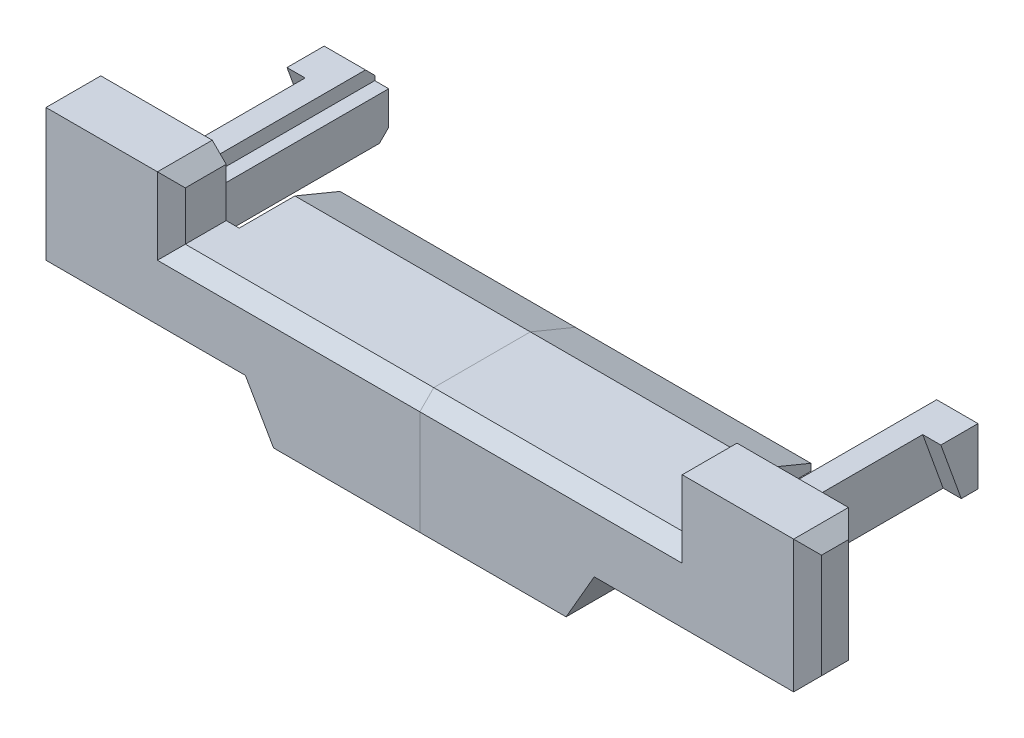
SolidWorks part; units mm, degrees
ref_plane "Płaszczyzna przednia" through (0, 0, 0) normal (0, 0, 1) x (1, 0, 0)
ref_plane "Płaszczyzna górna" through (0, 0, 0) normal (0, 1, 0) x (1, 0, 0)
ref_plane "Płaszczyzna prawa" through (0, 0, 0) normal (1, 0, 0) x (0, 0, -1)
sketch "Sketch1" plane through (0, 0, 0) normal (0, 0, 1) x (1, 0, 0)
  line L0 (-8.2, 0.6) -> (-8.2, 1.95)
  line L1 (-8.2, 1.95) -> (-11.2, 1.95)
  line L2 (-11.2, 1.95) -> (-11.2, -0.9)
  line L3 (-11.2, -0.9) -> (-6.6062, -0.9)
  line L4 (-6.6062, -0.9) -> (-6, -1.95)
  line L5 (-6, -1.95) -> (6, -1.95)
  line L6 (6, -1.95) -> (6.6062, -0.9)
  line L7 (6.6062, -0.9) -> (11.2, -0.9)
  line L8 (11.2, -0.9) -> (11.2, 1.95)
  line L9 (11.2, 1.95) -> (8.2, 1.95)
  line L10 (8.2, 1.95) -> (8.2, 0.6)
  line L11 (8.2, 0.6) -> (-8.2, 0.6)
extrude "Boss-Extrude1" add sketch "Sketch1" along normal blind 1.18
sketch "Sketch2" plane through (0, 0.6, 0) normal (0, 1, 0) x (1, 0, 0)
  line L0 (0, -1.18) -> (0, 2.17) construction
  line L1 (8.2, -1.18) -> (-8.2, -1.18) construction
  line L2 (7.92, 0) -> (7.92, 2.17)
  line L3 (8.2, 0) -> (-8.2, 0) construction
  line L4 (7.92, 2.17) -> (-7.92, 2.17)
  line L5 (-7.92, 2.17) -> (-7.92, 0)
  line L6 (8.2, -1.18) -> (8.2, 0) construction
  line L7 (7.92, 0) -> (-7.92, 0)
  dimension "D1" = 0.28
  dimension "D2" = 2.17
extrude "Boss-Extrude2" add sketch "Sketch2" against normal blind 0.55
sketch "Sketch3" plane through (-7.92, 0, 0) normal (-1, 0, 0) x (0, 0, 1)
  line L0 (-1.2, 0.6) -> (-2.17, 0.2)
  line L1 (-2.17, 0.6) -> (0, 0.6) construction
  line L2 (-2.17, 0.05) -> (-2.17, 0.6) construction
  line L3 (-2.17, 0.2) -> (-2.17, 0.6)
  line L4 (-2.17, 0.6) -> (-1.2, 0.6)
  dimension "D1" = 0.97
  dimension "D2" = 0.4
extrude "Cut-Extrude1" cut sketch "Sketch3" against normal through all both and the other way through all
chamfer "Chamfer1" distance 0.3 angle 45 8 edges at (11.2, -0.9, 0.59) (11.2, 0.525, 1.18) (11.2, 1.95, 0.59) (11.2, 0.525, 0) (-11.2, 1.95, 0.59) (-11.2, 0.525, 1.18) (-11.2, -0.9, 0.59) (-11.2, 0.525, 0)
chamfer "Chamfer2" distance 0.3 angle 45 5 edges at (-8.2, 1.95, 0.59) (-8.2, 1.275, 1.18) (8.2, 1.95, 0.59) (8.2, 1.275, 1.18) (0, 0.6, 1.18)
sketch "Sketch4" plane through (0, 0, 0) normal (0, 0, -1) x (-1, 0, 0)
  line L0 (-10.9, 1.95) -> (-8.5, 1.95) construction
  line L1 (-9.89, -0.11) -> (-8.7, -0.11)
  line L2 (-9.89, -0.11) -> (-9.89, 1.11)
  line L3 (-9.89, 1.11) -> (-8.7, 1.11)
  line L4 (-8.7, -0.11) -> (-8.7, 1.11)
  line L5 (-9.89, -0.11) -> (-8.7, 1.11) construction
  line L6 (-9.89, 1.11) -> (-8.7, -0.11) construction
  line L7 (-11.2, -0.6) -> (-11.2, 1.65) construction
  point P0 (-9.295, 0.5)
  dimension "D1" = 1.22
  dimension "D2" = 1.19
  dimension "D3" = 0.84
  dimension "D4" = 1.31
extrude "Boss-Extrude3" add sketch "Sketch4" along normal blind 4 separate body
sketch "Sketch5" plane through (0, 0, -4) normal (0, 0, -1) x (-1, 0, 0)
  line L0 (-9, 1.11) -> (-9, 0.81)
  line L1 (-8.7, 1.11) -> (-9.89, 1.11) construction
  line L2 (-9, 0.81) -> (-8.7, 0.81)
  line L3 (-8.7, -0.11) -> (-8.7, 1.11) construction
  line L4 (-8.7, 0.81) -> (-8.7, 1.11)
  line L5 (-8.7, 1.11) -> (-9, 1.11)
  dimension "D1" = 0.3
  dimension "D2" = 0.3
extrude "Cut-Extrude2" cut sketch "Sketch5" against normal up to surface (4 mm away) up to face at (0, 0.3389, 0)
chamfer "Chamfer3" distance 0.2 angle 45 3 edges at (9.295, -0.11, -4) (9.89, 0.5, -4) (9.445, 1.11, -4)
sketch "Sketch6" plane through (9.89, 0, 0) normal (1, 0, 0) x (0, 0, -1)
  line L0 (0, -0.11) -> (3.44, -0.11) construction
  line L1 (3.8, -0.11) -> (0, -0.11) construction
  line L2 (0, 1.11) -> (3, 1.11) construction
  line L3 (3.8, 1.11) -> (0, 1.11) construction
  line L4 (3.44, -0.11) -> (3, 1.11)
  line L5 (3.44, -0.11) -> (0, -0.11)
  line L6 (0, -0.11) -> (0, 1.11)
  line L7 (0, 1.11) -> (3, 1.11)
extrude "Cut-Extrude3" cut sketch "Sketch6" against normal blind 0.39
ref_plane "Plane1" through (0, 0, 0) normal (1, 0, 0) x (0, 0, -1)
mirror "Mirror1" about plane through (0, 0, 0) normal (1, 0, 0) of bodies 106
sketch "Szkic1" plane through (0, 0.6, 0) normal (0, 1, 0) x (1, 0, 0)
  line L1 (2.85, 3.48) -> (-2.85, 3.48)
  line L2 (2.85, 3.48) -> (2.85, -3.48)
  line L3 (2.85, -3.48) -> (-2.85, -3.48)
  line L4 (-2.85, 3.48) -> (-2.85, -3.48)
  line L5 (2.85, 3.48) -> (-2.85, -3.48) construction
  line L6 (2.85, -3.48) -> (-2.85, 3.48) construction
  point P0 (0, 0)
  dimension "D1" = 5.7
extrude "Wytnij-wyciągnięcie1" cut sketch "Szkic1" against normal through all
move or copy body "Obiekt-Przenieś/Kopiuj1" bodies to move or copy 109 106 copy no translate (-5.7, 0, 0) parameters "D1"=5.7, "D2"=0, "D3"=0
